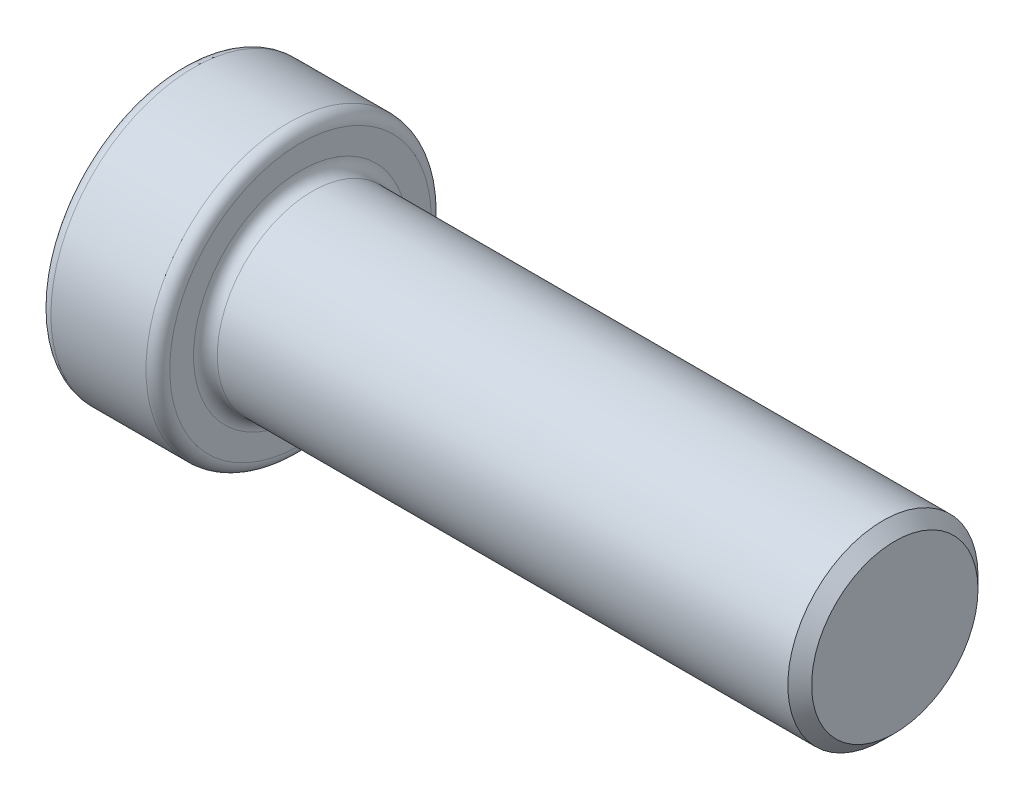
SolidWorks part; units mm, degrees
material "AISI 1020"
ref_plane "Alzado" through (0, 0, 0) normal (0, 0, 1) x (1, 0, 0)
ref_plane "Planta" through (0, 0, 0) normal (0, 1, 0) x (1, 0, 0)
ref_plane "Vista lateral" through (0, 0, 0) normal (1, 0, 0) x (0, 0, -1)
sketch "Croquis1" plane through (0, 0, 0) normal (0, 0, 1) x (1, 0, 0)
  line L0 (0, 0) -> (-29.2857, 0) construction
  line L1 (0, 0) -> (0, 4)
  line L2 (0, 4) -> (-25, 4)
  line L3 (-25, 4) -> (-25, 6)
  line L4 (-25, 6) -> (-30, 6)
  line L5 (-30, 6) -> (-30, 2.5)
  line L6 (-30, 2.5) -> (-5, 2.5)
  line L7 (-5, 2.5) -> (-5, 0)
  line L8 (0, 0) -> (-5, 0)
  dimension "D1" = 5
  dimension "D2" = 25
  dimension "D3" = 8
  dimension "D4" = 12
  dimension "D5" = 5
  dimension "D6" = 5
revolve "Revolución1" add sketch "Croquis1" angle 360 about L0
chamfer "Chaflán1" distance 0.5 angle 45 2 edges at (-30, 0, -2.5) (0, 0, -4)
fillet "Redondeo1" radius 0.5 3 edges at (-25, 0, -4) (-25, 0, -6) (-30, 0, -6)
